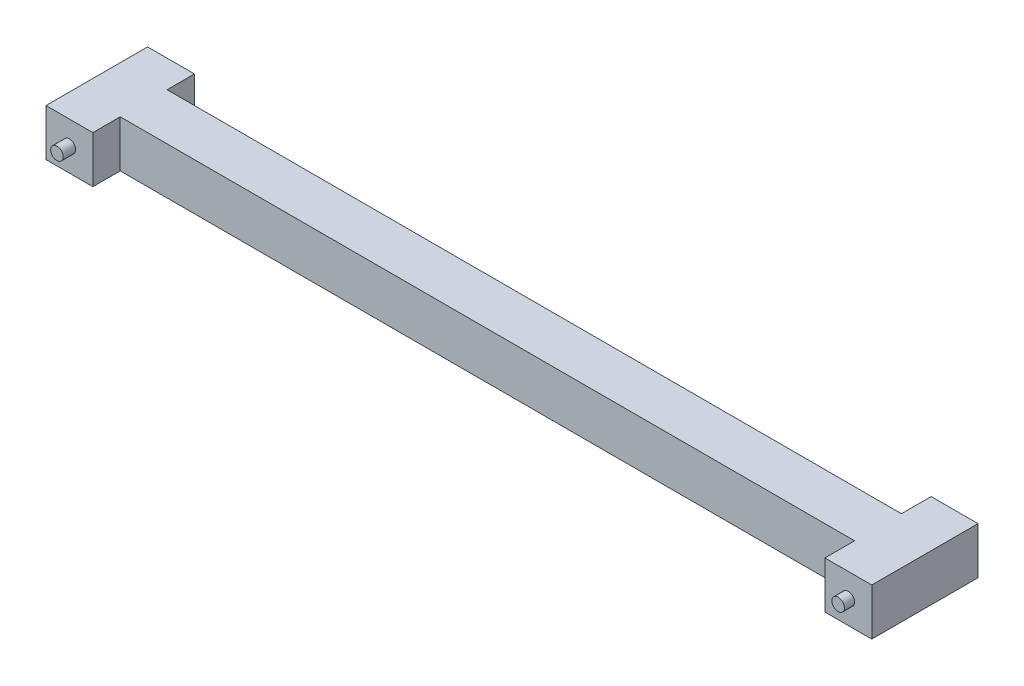
SolidWorks part; units mm, degrees
ref_plane "前视基准面" through (0, 0, 0) normal (0, 0, 1) x (1, 0, 0)
ref_plane "上视基准面" through (0, 0, 0) normal (0, 1, 0) x (1, 0, 0)
ref_plane "右视基准面" through (0, 0, 0) normal (1, 0, 0) x (0, 0, -1)
sketch "草图1" plane through (0, 0, 0) normal (0, 0, 1) x (1, 0, 0)
  line L1 (-4.5909, -0.4272) -> (1.4091, -0.4272)
  line L2 (-4.5909, -0.4272) -> (-4.5909, -6.4272)
  line L3 (-4.5909, -6.4272) -> (1.4091, -6.4272)
  line L4 (1.4091, -0.4272) -> (1.4091, -6.4272)
extrude "凸台-拉伸1" add sketch "草图1" along normal blind 13
sketch "草图3" plane through (0, 0, 0) normal (0, 0, -1) x (-1, 0, 0)
  circle A0 centre (1.5909, -3.4272) radius 0.8
extrude "凸台-拉伸3" add sketch "草图3" along normal blind 1.6
sketch "草图4" plane through (1.4091, 0, 0) normal (1, 0, 0) x (0, 0, -1)
  line L0 (-13, -3.4272) -> (0, -3.4272)
  line L1 (-13, -6.4272) -> (-13, -0.4272) construction
  line L2 (0, -4.2272) -> (0, -2.6272) construction
  line L3 (-13, -6.4272) -> (0, -6.4272) construction
  line L4 (-9.5, -0.4272) -> (-3.5, -0.4272)
  line L5 (-9.5, -0.4272) -> (-9.5, -6.4272)
  line L6 (-9.5, -6.4272) -> (-3.5, -6.4272)
  line L7 (-3.5, -0.4272) -> (-3.5, -6.4272)
  line L8 (-9.5, -0.4272) -> (-3.5, -6.4272) construction
  line L9 (-9.5, -6.4272) -> (-3.5, -0.4272) construction
  point P6 (-6.5, -3.4272)
  line M5 (0, -0.4272) -> (-13, -0.4272)
  line M7 (-13, -6.4272) -> (0, -6.4272)
extrude "凸台-拉伸4" add sketch "草图4" along normal blind 94 contours L7 L0 L5 M7 | L7 L5 L0 M5
sketch "草图5" plane through (95.4091, 0, 0) normal (1, 0, 0) x (0, 0, -1)
  line L1 (-13.3, -0.4272) -> (0.3, -0.4272)
  line L2 (-13.3, -0.4272) -> (-13.3, -6.4272)
  line L3 (-13.3, -6.4272) -> (0.3, -6.4272)
  line L4 (0.3, -0.4272) -> (0.3, -6.4272)
extrude "凸台-拉伸5" add sketch "草图5" along normal blind 6
sketch "草图2" plane through (0, 0, 13) normal (0, 0, 1) x (1, 0, 0)
  circle A0 centre (-1.5909, -3.4272) radius 0.8
  circle A1 centre (98.4091, -3.4272) radius 0.8
extrude "凸台-拉伸2" add sketch "草图2" along normal blind 1.6
sketch "草图7" plane through (0, 0, -0.3) normal (0, 0, -1) x (-1, 0, 0)
  circle A0 centre (-98.4091, -3.4272) radius 0.8
extrude "凸台-拉伸6" add sketch "草图7" along normal blind 1.6
